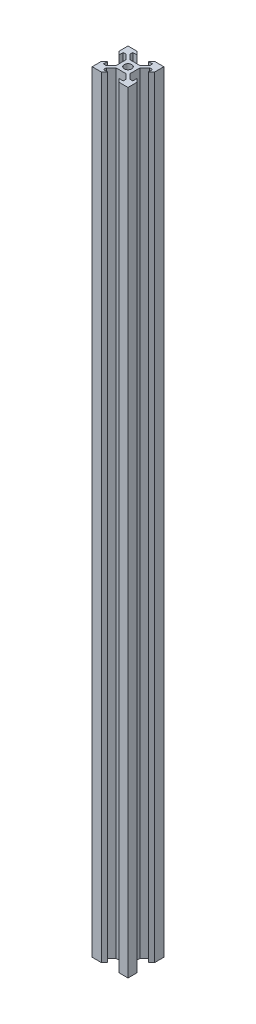
SolidWorks part; units mm, degrees
material "6061-T6 (SS)"
ref_plane "前视基准面" through (0, 0, 0) normal (0, 0, 1) x (1, 0, 0)
ref_plane "上视基准面" through (0, 0, 0) normal (0, 1, 0) x (1, 0, 0)
ref_plane "右视基准面" through (0, 0, 0) normal (1, 0, 0) x (0, 0, -1)
sketch "草图1" plane through (0, 0, 0) normal (0, 1, 0) x (1, 0, 0)
  line L0 (-10, 10) -> (-4.9, 10)
  line L1 (-10, -10) -> (10, -10) construction
  line L2 (-10, -10) -> (-10, 10) construction
  line L3 (-10, 10) -> (10, 10) construction
  line L4 (10, -10) -> (10, 10) construction
  line L5 (-10, -10) -> (10, 10) construction
  line L6 (-10, 10) -> (10, -10) construction
  line L7 (-4.9, 10) -> (-3.1, 8.2)
  line L8 (-3.1, 8.2) -> (-5.5, 8.2)
  line L9 (-5.5, 8.2) -> (-5.5, 6.5607)
  line L10 (-5.5, 6.5607) -> (-2.8393, 3.9)
  line L11 (-2.8393, 3.9) -> (0, 3.9)
  line L12 (0, 0) -> (0, 10) construction
  line L13 (-3.9, 2.8393) -> (-3.9, -2.8393)
  line L14 (-6.5607, 5.5) -> (-3.9, 2.8393)
  line L15 (-8.2, 5.5) -> (-6.5607, 5.5)
  line L16 (-8.2, 3.1) -> (-8.2, 5.5)
  line L17 (-10, 4.9) -> (-8.2, 3.1)
  line L18 (-10, 10) -> (-10, 4.9)
  line L19 (2.8393, 3.9) -> (0, 3.9)
  line L20 (10, 10) -> (10, 4.9)
  line L21 (10, 4.9) -> (8.2, 3.1)
  line L22 (8.2, 3.1) -> (8.2, 5.5)
  line L23 (8.2, 5.5) -> (6.5607, 5.5)
  line L24 (6.5607, 5.5) -> (3.9, 2.8393)
  line L25 (3.9, 2.8393) -> (3.9, -2.8393)
  line L26 (5.5, 6.5607) -> (2.8393, 3.9)
  line L27 (5.5, 8.2) -> (5.5, 6.5607)
  line L28 (3.1, 8.2) -> (5.5, 8.2)
  line L29 (4.9, 10) -> (3.1, 8.2)
  line L30 (10, 10) -> (4.9, 10)
  line L31 (-10, 0) -> (10, 0) construction
  line L32 (10, -10) -> (10, -4.9)
  line L33 (10, -10) -> (4.9, -10)
  line L34 (4.9, -10) -> (3.1, -8.2)
  line L35 (-4.9, -10) -> (-3.1, -8.2)
  line L36 (-10, -10) -> (-4.9, -10)
  line L37 (-10, -10) -> (-10, -4.9)
  line L38 (3.1, -8.2) -> (5.5, -8.2)
  line L39 (5.5, -8.2) -> (5.5, -6.5607)
  line L40 (5.5, -6.5607) -> (2.8393, -3.9)
  line L41 (6.5607, -5.5) -> (3.9, -2.8393)
  line L42 (8.2, -5.5) -> (6.5607, -5.5)
  line L43 (8.2, -3.1) -> (8.2, -5.5)
  line L44 (10, -4.9) -> (8.2, -3.1)
  line L45 (2.8393, -3.9) -> (0, -3.9)
  line L46 (-10, -4.9) -> (-8.2, -3.1)
  line L47 (-8.2, -3.1) -> (-8.2, -5.5)
  line L48 (-8.2, -5.5) -> (-6.5607, -5.5)
  line L49 (-6.5607, -5.5) -> (-3.9, -2.8393)
  line L50 (-2.8393, -3.9) -> (0, -3.9)
  line L51 (-5.5, -6.5607) -> (-2.8393, -3.9)
  line L52 (-5.5, -8.2) -> (-5.5, -6.5607)
  line L53 (-3.1, -8.2) -> (-5.5, -8.2)
  circle A0 centre (0, 0) radius 2.1
  point P0 (0, 0)
  point P23 (-1.4197, 3.9)
  point P24 (1.4197, 3.9)
  point P42 (-3.9, 0)
  point P43 (3.9, 0)
  point P56 (1.4197, -3.9)
  dimension "D9" = 4.2
  dimension "D1" = 20
  dimension "D2" = 20
  dimension "D3" = 0.75
  dimension "D4" = 1.8
  dimension "D5" = 4.9
  dimension "D6" = 3.1
  dimension "D7" = 5.5
  dimension "D8" = 6.1
extrude "凸台-拉伸1" add sketch "草图1" along normal blind 430
